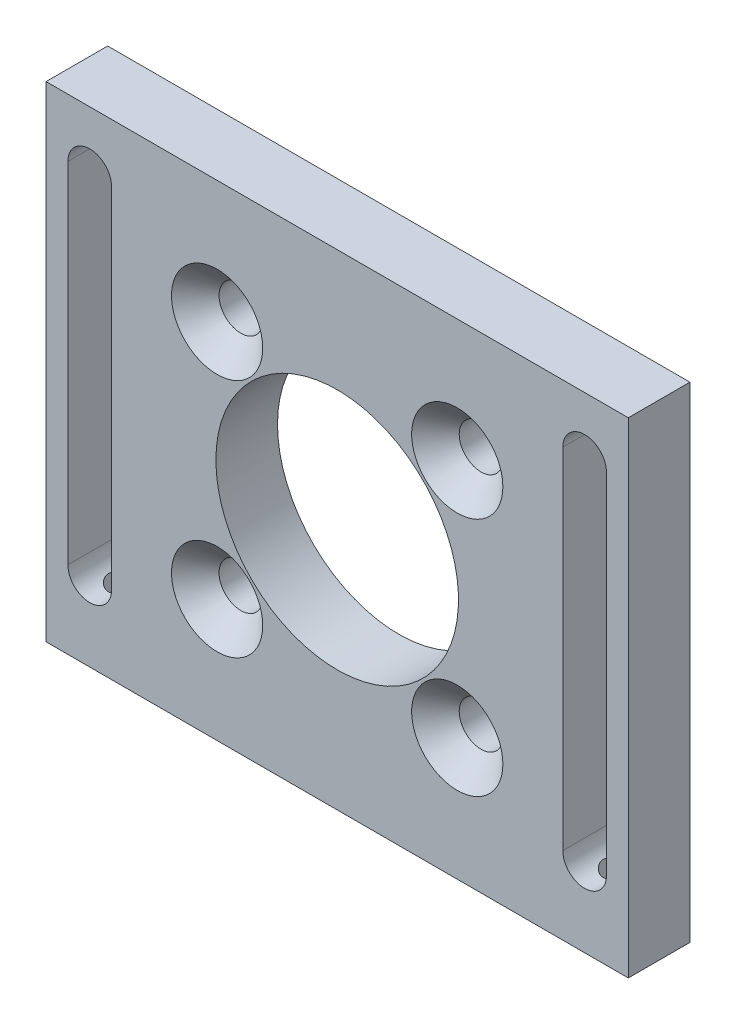
SolidWorks part; units mm, degrees
material "Onyx"
ref_plane "Front Plane" through (0, 0, 0) normal (0, 0, 1) x (1, 0, 0)
ref_plane "Top Plane" through (0, 0, 0) normal (0, 1, 0) x (1, 0, 0)
ref_plane "Right Plane" through (0, 0, 0) normal (1, 0, 0) x (0, 0, -1)
ref_plane "Plane1" through (0, 0, 0) normal (0, 0, -1) x (-1, 0, 0)
sketch "Sketch1" plane through (0, 0, 0) normal (0, 0, -1) x (-1, 0, 0)
  line L0 (-30, -25) -> (30, -25)
  line L1 (30, -25) -> (30, 25)
  line L2 (30, 25) -> (-30, 25)
  line L3 (-30, 25) -> (-30, -25)
extrude "Boss-Extrude1" add sketch "Sketch1" against normal blind 6.35
sketch "Sketch2" plane through (0, 0, 0) normal (0, 0, -1) x (-1, 0, 0)
  line L0 (23.25, 19) -> (23.25, -17)
  line L1 (27.75, -17) -> (27.75, 19)
  arc A0 (23.25, -17) -> (27.75, -17) centre (25.5, -17) ccw
  arc A1 (27.75, 19) -> (23.25, 19) centre (25.5, 19) ccw
extrude "Cut-Extrude1" cut sketch "Sketch2" against normal through all
sketch "Sketch3" plane through (0, 0, 6.35) normal (0, 0, 1) x (1, 0, 0)
  line L0 (27.75, -17) -> (27.75, 19)
  line L1 (23.25, 19) -> (23.25, -17)
  arc A0 (27.75, 19) -> (23.25, 19) centre (25.5, 19) ccw
  arc A1 (23.25, -17) -> (27.75, -17) centre (25.5, -17) ccw
extrude "Cut-Extrude2" cut sketch "Sketch3" against normal through all
hole_wizard "Hole1" positions "Sketch5" profile "Sketch4" legacy end condition through all
sketch "Sketch5" plane through (0, 0, 0) normal (0, 0, -1) x (-1, 0, 0)
  point P0 (0, 0)
sketch "Sketch4" plane through (0, 0, 0) normal (1, 0, 0) x (0, 1, 0)
  line L0 (0, 0) -> (0, 6.35)
  line L1 (0, 6.35) -> (12.5, 6.35)
  line L2 (12.5, 6.35) -> (12.5, 0)
  line L3 (12.5, 0) -> (0, 0)
  line L4 (0, 110) -> (0, -10) construction
  dimension "Diameter" = 25
  dimension "Depth" = 6.35
hole_wizard "#2 Clearance Hole1" positions "Sketch9" profile "Sketch8" hole size "#2" standard "ANSI Inch"
sketch "Sketch9" plane through (0, -25, 0) normal (0, -1, 0) x (-1, 0, 0)
  point P0 (-25.5, -3.175)
  point P1 (25.5, -3.175)
sketch "Sketch8" plane through (25.5, -25, 3.175) normal (1, 0, 0) x (0, 0, -1)
  line L0 (0, 0) -> (0, 5.75)
  line L1 (0, 5.75) -> (1.25, 5.75)
  line L2 (1.25, 5.75) -> (1.25, 0)
  line L5 (1.25, 0) -> (0, 0)
  line L11 (0, -6.35) -> (0, 107.95) construction
  dimension "Thru Hole Dia." = 2.5
  dimension "Thru Hole Depth" = 5.75
sketch "Sketch12" plane through (0, 0, 0) normal (0, 0, -1) x (-1, 0, 0)
  line L0 (0, 0) -> (-16.6665, 16.6665) construction
  line L1 (0, 0) -> (16.6665, 16.6665) construction
  line L2 (0, 0) -> (16.6665, -16.6665) construction
  line L3 (0, 0) -> (-16.6665, -16.6665) construction
  circle A0 centre (0, 0) radius 23.57 construction
  dimension "D1" = 47.14
hole_wizard "#8 Clearance Hole1" positions "Sketch13" profile "Sketch14" hole size "#8" standard "ANSI Inch" end condition through all
sketch "Sketch13" plane through (0, 0, 0) normal (0, 0, -1) x (-1, 0, 0)
  point P0 (-12.3744, 12.3744)
  point P3 (-12.3744, -12.3744)
  point P6 (12.3744, -12.3744)
  point P9 (12.3744, 12.3744)
  dimension "D1" = 17.5
  dimension "D2" = 17.5
sketch "Sketch14" plane through (12.3744, 12.3744, 0) normal (1, 0, 0) x (0, 1, 0)
  line L0 (0, 0) -> (0, 6.35)
  line L1 (0, 6.35) -> (2.25, 6.35)
  line L2 (2.25, 6.35) -> (2.25, 0)
  line L5 (2.25, 0) -> (0, 0)
  line L11 (0, -6.35) -> (0, 107.95) construction
  dimension "Thru Hole Dia." = 4.5
  dimension "Thru Hole Depth" = 6.35
chamfer "Chamfer1" distance 2.45 angle 45 4 edges at (10.1244, -12.3744, 6.35) (10.1244, 12.3744, 6.35) (-14.6244, 12.3744, 6.35) (-14.6244, -12.3744, 6.35)
